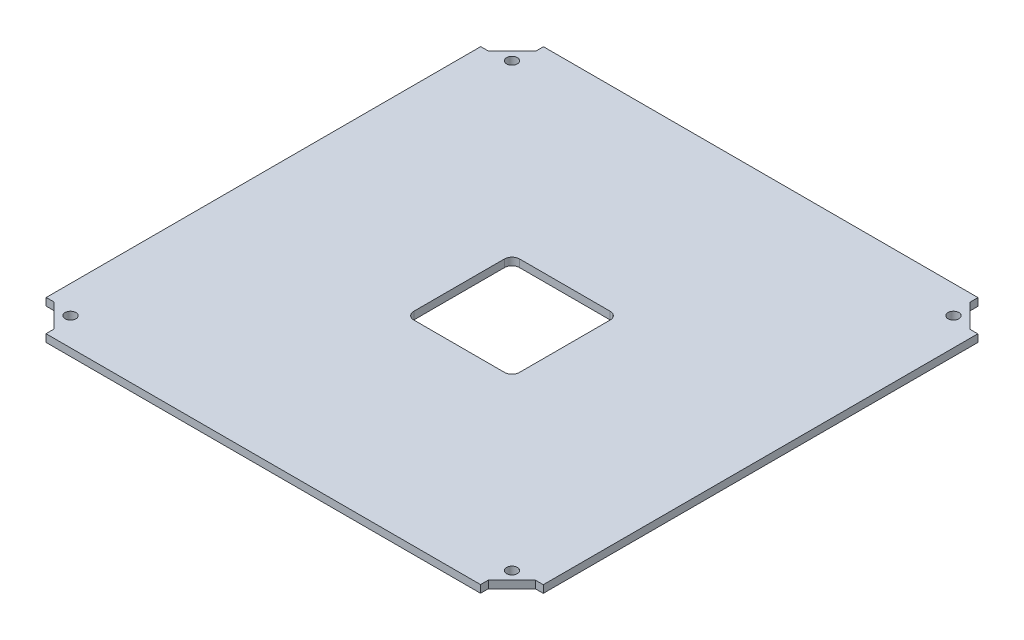
SolidWorks part; units mm, degrees
ref_plane "Front Plane" through (0, 0, 0) normal (0, 0, 1) x (1, 0, 0)
ref_plane "Top Plane" through (0, 0, 0) normal (0, 1, 0) x (1, 0, 0)
ref_plane "Right Plane" through (0, 0, 0) normal (1, 0, 0) x (0, 0, -1)
sketch "Sketch1" plane through (0, 0, 0) normal (0, 1, 0) x (1, 0, 0)
  line L0 (-91.2333, 104.4575) -> (-91.2333, 101.1555)
  line L1 (-91.3214, -104.4575) -> (91.2333, -104.4575)
  line L2 (-104.4575, -91.2333) -> (-104.4575, 91.3214)
  line L3 (-91.2333, 104.4575) -> (91.3214, 104.4575)
  line L4 (104.4575, -91.3214) -> (104.4575, 91.2333)
  line L5 (-117.475, -117.475) -> (117.475, 117.475) construction
  line L6 (-117.475, 117.475) -> (117.475, -117.475) construction
  line L7 (-101.1555, 91.3214) -> (-91.2333, 101.1555)
  line L8 (-104.4575, 91.3214) -> (-101.1555, 91.3214)
  line L9 (-104.4575, 91.3214) -> (-104.4575, 104.4575)
  line L10 (-104.4575, 104.4575) -> (-91.2333, 104.4575)
  line L11 (91.3214, 104.4575) -> (104.4575, 104.4575)
  line L12 (104.4575, 104.4575) -> (104.4575, 91.2333)
  line L13 (91.3214, 104.4575) -> (91.3214, 101.1555)
  line L14 (104.4575, 91.2333) -> (101.1555, 91.2333)
  line L15 (104.4575, -91.3214) -> (101.1555, -91.3214)
  line L16 (91.2333, -104.4575) -> (91.2333, -101.1555)
  line L17 (-91.3214, -104.4575) -> (-91.3214, -101.1555)
  line L18 (-104.4575, -91.2333) -> (-101.1555, -91.2333)
  line L19 (91.3214, 101.1555) -> (101.1555, 91.2333)
  line L20 (91.2333, -101.1555) -> (101.1555, -91.3214)
  line L21 (-101.1555, -91.2333) -> (-91.3214, -101.1555)
  line L22 (91.2333, -104.4575) -> (104.4575, -104.4575)
  line L23 (104.4575, -104.4575) -> (104.4575, -91.3214)
  line L24 (-104.4575, -91.2333) -> (-104.4575, -104.4575)
  line L25 (-104.4575, -104.4575) -> (-91.3214, -104.4575)
  point P0 (0, 0)
  dimension "D2" = 3.302
  dimension "D3" = 3.302
  dimension "D4" = 13.97
  dimension "D5" = 208.915
  dimension "D6" = 104.4575
  dimension "D7" = 13.97
  dimension "D8" = 104.4575
  dimension "D9" = 13.97
  dimension "D10" = 13.2242
  dimension "D11" = 13.97
  dimension "D12" = 208.915
extrude "Boss-Extrude1" add sketch "Sketch1" along normal blind 3.175
sketch "Sketch3" plane through (0, 3.175, 0) normal (0, 1, 0) x (1, 0, 0)
  line L0 (-92.7341, 92.7341) -> (92.7341, 92.7341)
  line L1 (92.7341, 92.7341) -> (92.7341, -92.7341)
  line L2 (92.7341, -92.7341) -> (-92.7341, -92.7341)
  line L3 (-92.7341, -92.7341) -> (-92.7341, 92.7341)
  line L19 (-91.3214, -104.4575) -> (91.2333, -104.4575)
  line L21 (-104.4575, -91.2333) -> (-101.1555, -91.2333)
  line L22 (-104.4575, -91.2333) -> (-101.1555, -91.2333)
  line L23 (104.4575, -91.3214) -> (104.4575, 91.2333)
  line L24 (-101.1555, -91.2333) -> (-91.3214, -101.1555)
  line L25 (-101.1555, -91.2333) -> (-91.3214, -101.1555)
  line L26 (-91.3214, -101.1555) -> (-91.3214, -104.4575)
  line L27 (91.3214, 104.4575) -> (-91.2333, 104.4575)
  line L28 (-91.3214, -101.1555) -> (-91.3214, -104.4575)
  line L29 (91.2333, -104.4575) -> (91.2333, -101.1555)
  line L30 (91.2333, -104.4575) -> (91.2333, -101.1555)
  line L31 (-104.4575, 91.3214) -> (-104.4575, -91.2333)
  line L35 (-91.3214, -104.4575) -> (91.2333, -104.4575)
  line L39 (104.4575, -91.3214) -> (104.4575, 91.2333)
  line L43 (91.3214, 104.4575) -> (-91.2333, 104.4575)
  line L47 (-104.4575, 91.3214) -> (-104.4575, -91.2333)
  line L48 (91.2333, -101.1555) -> (101.1555, -91.3214)
  line L49 (91.2333, -101.1555) -> (101.1555, -91.3214)
  line L50 (101.1555, -91.3214) -> (104.4575, -91.3214)
  line L51 (101.1555, -91.3214) -> (104.4575, -91.3214)
  line L52 (104.4575, 91.2333) -> (101.1555, 91.2333)
  line L53 (104.4575, 91.2333) -> (101.1555, 91.2333)
  line L54 (101.1555, 91.2333) -> (91.3214, 101.1555)
  line L55 (101.1555, 91.2333) -> (91.3214, 101.1555)
  line L56 (91.3214, 101.1555) -> (91.3214, 104.4575)
  line L57 (91.3214, 101.1555) -> (91.3214, 104.4575)
  line L58 (-91.2333, 104.4575) -> (-91.2333, 101.1555)
  line L59 (-91.2333, 104.4575) -> (-91.2333, 101.1555)
  line L60 (-91.2333, 101.1555) -> (-101.1555, 91.3214)
  line L61 (-91.2333, 101.1555) -> (-101.1555, 91.3214)
  line L62 (-101.1555, 91.3214) -> (-104.4575, 91.3214)
  line L63 (-101.1555, 91.3214) -> (-104.4575, 91.3214)
  circle A0 centre (-92.7341, 92.7341) radius 2.286
  circle A1 centre (92.7341, 92.7341) radius 2.286
  circle A2 centre (92.7341, -92.7341) radius 2.286
  circle A3 centre (-92.7341, -92.7341) radius 2.286
  point P7 (0, 0)
  point P13 (46.5305, 89.4025)
  point P18 (0, 92.7341)
  point P20 (-92.7341, 0)
  dimension "D2" = 4.572
  dimension "D3" = 185.4683
  dimension "D4" = 104.4575
  dimension "D5" = 104.4575
  dimension "D1" = 0
extrude "Cut-Extrude1" cut sketch "Sketch3" against normal up to next contours A0 | A1 | A2 | A3
sketch "Sketch4" plane through (0, 3.175, 0) normal (0, 1, 0) x (1, 0, 0)
  line L0 (-104.4575, 91.3214) -> (-104.4575, 104.4575)
  line L1 (-104.4575, 104.4575) -> (-91.2333, 104.4575)
  line L2 (91.3214, 104.4575) -> (104.4575, 104.4575)
  line L3 (104.4575, 104.4575) -> (104.4575, 91.2333)
  line L4 (91.2333, -104.4575) -> (104.4575, -104.4575)
  line L5 (104.4575, -104.4575) -> (104.4575, -91.3214)
  line L6 (-104.4575, -91.2333) -> (-104.4575, -104.4575)
  line L7 (-91.3214, -104.4575) -> (-104.4575, -104.4575)
  line L16 (-104.4575, -91.2333) -> (-101.1555, -91.2333)
  line L17 (-101.1555, -91.2333) -> (-91.3214, -101.1555)
  line L18 (-91.3214, -101.1555) -> (-91.3214, -104.4575)
  line L19 (-91.3214, -104.4575) -> (91.2333, -104.4575)
  line L20 (91.2333, -104.4575) -> (91.2333, -101.1555)
  line L21 (91.2333, -101.1555) -> (101.1555, -91.3214)
  line L22 (101.1555, -91.3214) -> (104.4575, -91.3214)
  line L23 (104.4575, -91.3214) -> (104.4575, 91.2333)
  line L24 (104.4575, 91.2333) -> (101.1555, 91.2333)
  line L25 (101.1555, 91.2333) -> (91.3214, 101.1555)
  line L26 (91.3214, 101.1555) -> (91.3214, 104.4575)
  line L27 (91.3214, 104.4575) -> (-91.2333, 104.4575)
  line L28 (-91.2333, 104.4575) -> (-91.2333, 101.1555)
  line L29 (-91.2333, 101.1555) -> (-101.1555, 91.3214)
  line L30 (-101.1555, 91.3214) -> (-104.4575, 91.3214)
  line L31 (-104.4575, 91.3214) -> (-104.4575, -91.2333)
  line L32 (-104.4575, -91.2333) -> (-101.1555, -91.2333)
  line L33 (-101.1555, -91.2333) -> (-91.3214, -101.1555)
  line L34 (-91.3214, -101.1555) -> (-91.3214, -104.4575)
  line L36 (91.2333, -104.4575) -> (91.2333, -101.1555)
  line L37 (91.2333, -101.1555) -> (101.1555, -91.3214)
  line L38 (101.1555, -91.3214) -> (104.4575, -91.3214)
  line L40 (104.4575, 91.2333) -> (101.1555, 91.2333)
  line L41 (101.1555, 91.2333) -> (91.3214, 101.1555)
  line L42 (91.3214, 101.1555) -> (91.3214, 104.4575)
  line L44 (-91.2333, 104.4575) -> (-91.2333, 101.1555)
  line L45 (-91.2333, 101.1555) -> (-101.1555, 91.3214)
  line L46 (-101.1555, 91.3214) -> (-104.4575, 91.3214)
  point P8 (0, 0)
  point P12 (0, 0)
  dimension "D1" = 0
sketch "Sketch5" plane through (0, 3.175, 0) normal (0, 1, 0) x (1, 0, 0)
  line L1 (22.225, -22.225) -> (-22.225, -22.225)
  line L2 (22.225, -22.225) -> (22.225, 22.225)
  line L3 (22.225, 22.225) -> (-22.225, 22.225)
  line L4 (-22.225, -22.225) -> (-22.225, 22.225)
  line L5 (22.225, -22.225) -> (-22.225, 22.225) construction
  line L6 (22.225, 22.225) -> (-22.225, -22.225) construction
  line L16 (-104.4575, -91.2333) -> (-101.1555, -91.2333)
  line L17 (-101.1555, -91.2333) -> (-91.3214, -101.1555)
  line L18 (-91.3214, -101.1555) -> (-91.3214, -104.4575)
  line L19 (-91.3214, -104.4575) -> (91.2333, -104.4575)
  line L20 (91.2333, -104.4575) -> (91.2333, -101.1555)
  line L21 (91.2333, -101.1555) -> (101.1555, -91.3214)
  line L22 (101.1555, -91.3214) -> (104.4575, -91.3214)
  line L23 (104.4575, -91.3214) -> (104.4575, 91.2333)
  line L24 (104.4575, 91.2333) -> (101.1555, 91.2333)
  line L25 (101.1555, 91.2333) -> (91.3214, 101.1555)
  line L26 (91.3214, 101.1555) -> (91.3214, 104.4575)
  line L27 (91.3214, 104.4575) -> (-91.2333, 104.4575)
  line L28 (-91.2333, 104.4575) -> (-91.2333, 101.1555)
  line L29 (-91.2333, 101.1555) -> (-101.1555, 91.3214)
  line L30 (-101.1555, 91.3214) -> (-104.4575, 91.3214)
  line L31 (-104.4575, 91.3214) -> (-104.4575, -91.2333)
  line L32 (-104.4575, -91.2333) -> (-101.1555, -91.2333)
  line L33 (-101.1555, -91.2333) -> (-91.3214, -101.1555)
  line L34 (-91.3214, -101.1555) -> (-91.3214, -104.4575)
  line L35 (-91.3214, -104.4575) -> (91.2333, -104.4575)
  line L36 (91.2333, -104.4575) -> (91.2333, -101.1555)
  line L37 (91.2333, -101.1555) -> (101.1555, -91.3214)
  line L38 (101.1555, -91.3214) -> (104.4575, -91.3214)
  line L39 (104.4575, -91.3214) -> (104.4575, 91.2333)
  line L40 (104.4575, 91.2333) -> (101.1555, 91.2333)
  line L41 (101.1555, 91.2333) -> (91.3214, 101.1555)
  line L42 (91.3214, 101.1555) -> (91.3214, 104.4575)
  line L43 (91.3214, 104.4575) -> (-91.2333, 104.4575)
  line L44 (-91.2333, 104.4575) -> (-91.2333, 101.1555)
  line L45 (-91.2333, 101.1555) -> (-101.1555, 91.3214)
  line L46 (-101.1555, 91.3214) -> (-104.4575, 91.3214)
  line L47 (-104.4575, 91.3214) -> (-104.4575, -91.2333)
  point P2 (0, 0)
  dimension "D2" = 44.45
  dimension "D1" = 0
extrude "Cut-Extrude2" cut sketch "Sketch5" against normal up to next contours L4 L1 L2 L3
fillet "Fillet1" radius 3.175 4 edges at (22.225, 1.5875, -22.225) (-22.225, 1.5875, -22.225) (-22.225, 1.5875, 22.225) (22.225, 1.5875, 22.225)
